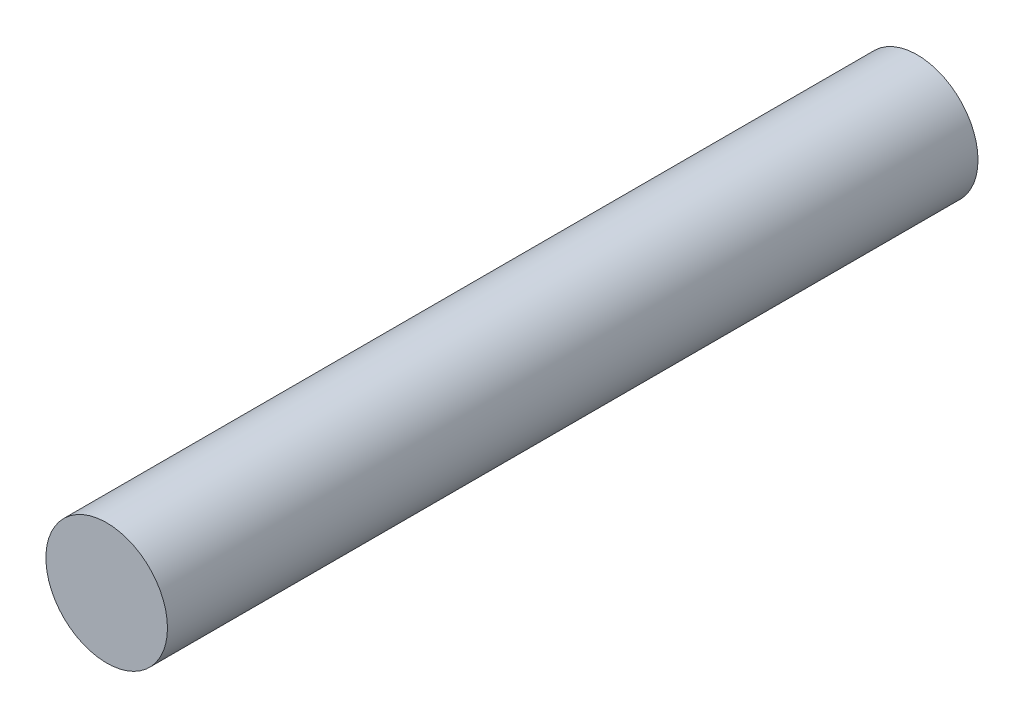
SolidWorks part; units mm, degrees
material "Stainless Steel (ferritic)"
ref_plane "Front Plane" through (0, 0, 0) normal (0, 0, 1) x (1, 0, 0)
ref_plane "Top Plane" through (0, 0, 0) normal (0, 1, 0) x (1, 0, 0)
ref_plane "Right Plane" through (0, 0, 0) normal (1, 0, 0) x (0, 0, -1)
sketch "Sketch1" plane through (0, 0, 0) normal (0, 0, 1) x (1, 0, 0)
  circle A0 centre (0, 0) radius 4.7625
  dimension "D1" = 9.525
extrude "Boss-Extrude1" add sketch "Sketch1" along normal blind 63.5
